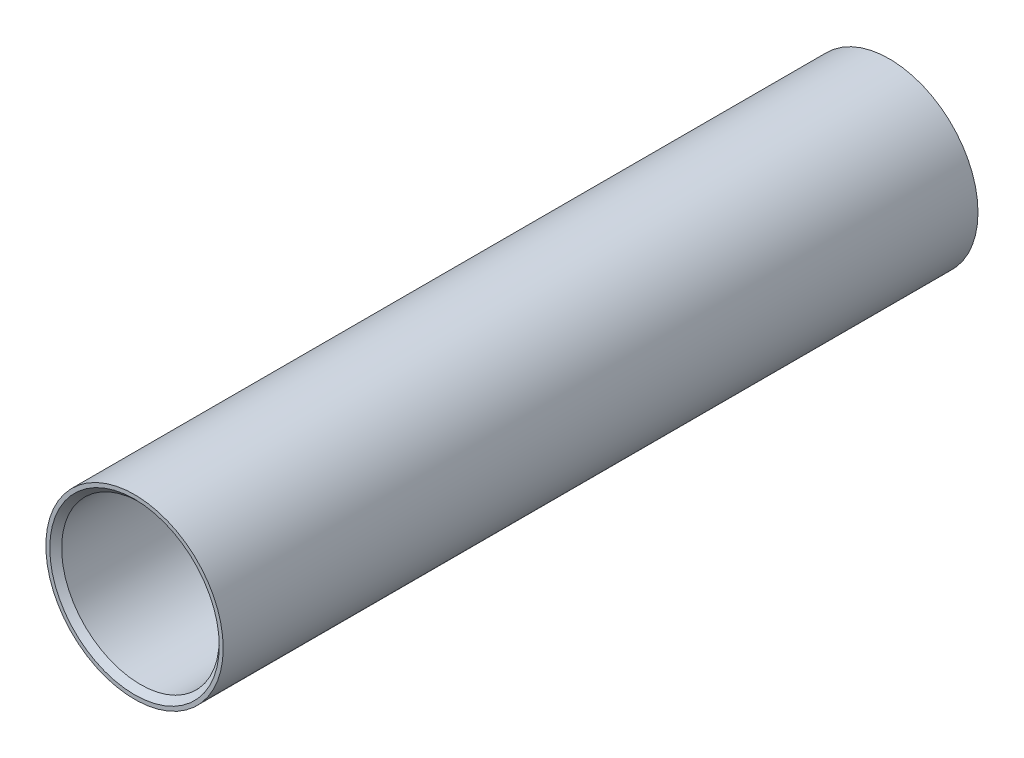
SolidWorks part; units mm, degrees
ref_plane "Front Plane" through (0, 0, 0) normal (0, 0, 1) x (1, 0, 0)
ref_plane "Top Plane" through (0, 0, 0) normal (0, 1, 0) x (1, 0, 0)
ref_plane "Right Plane" through (0, 0, 0) normal (1, 0, 0) x (0, 0, -1)
sketch "Sketch1" plane through (0, 0, 0) normal (1, 0, 0) x (0, 0, -1)
  line L0 (0, 0) -> (0, 6416.7499) construction
  line L1 (0, 0) -> (6416.7499, 0) construction
  line L3 (-19.15, 4.5) -> (19.15, 4.5)
  line L4 (-19.15, 4.5) -> (-19.15, 4.3)
  line L5 (-18.85, 4) -> (18.85, 4)
  line L6 (19.15, 4.5) -> (19.15, 4.3)
  line L7 (18.85, 4) -> (19.15, 4.3)
  line L8 (-19.15, 4.3) -> (-18.85, 4)
  point P6 (19.15, 4)
  point P16 (-19.15, 4)
  dimension "L" = 38.3
  dimension "D2" = 45
  dimension "Ø1" = 8
  dimension "Ø2" = 9
  dimension "C1" = 0.3
  dimension "D7" = 45
  dimension "C2" = 0.3
revolve "Revolve1" add sketch "Sketch1" angle 360 about L1
